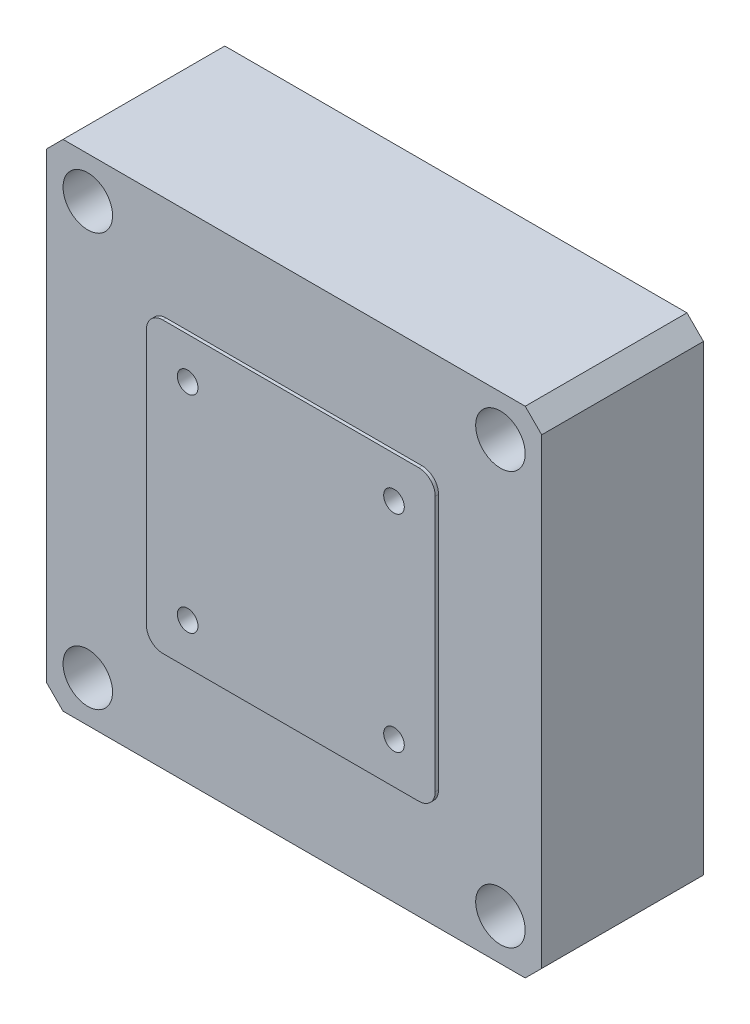
SolidWorks part; units mm, degrees
ref_plane "前视基准面" through (0, 0, 0) normal (0, 0, 1) x (1, 0, 0)
ref_plane "上视基准面" through (0, 0, 0) normal (0, 1, 0) x (1, 0, 0)
ref_plane "右视基准面" through (0, 0, 0) normal (1, 0, 0) x (0, 0, -1)
sketch "草图1" plane through (0, 0, 0) normal (0, 0, 1) x (1, 0, 0)
  line L1 (-30, 30) -> (30, 30)
  line L2 (-30, 30) -> (-30, -30)
  line L3 (-30, -30) -> (30, -30)
  line L4 (30, 30) -> (30, -30)
  line L5 (-30, 30) -> (30, -30) construction
  line L6 (-30, -30) -> (30, 30) construction
  point P0 (0, 0)
  dimension "D1" = 60
extrude "凸台-拉伸1" add sketch "草图1" along normal blind 19.6
chamfer "倒角1" distance 2 angle 45 4 edges at (-30, -30, 9.8) (30, -30, 9.8) (30, 30, 9.8) (-30, 30, 9.8)
sketch "草图2" plane through (0, 0, 19.6) normal (0, 0, 1) x (1, 0, 0)
  line L1 (-17.5, 17.5) -> (17.5, 17.5)
  line L2 (-17.5, 17.5) -> (-17.5, -17.5)
  line L3 (-17.5, -17.5) -> (17.5, -17.5)
  line L4 (17.5, 17.5) -> (17.5, -17.5)
  line L5 (-17.5, 17.5) -> (17.5, -17.5) construction
  line L6 (-17.5, -17.5) -> (17.5, 17.5) construction
  point P0 (0, 0)
  dimension "D1" = 35
extrude "凸台-拉伸2" add sketch "草图2" along normal blind 0.4
fillet "圆角1" radius 2 4 edges at (17.5, -17.5, 19.8) (-17.5, -17.5, 19.8) (17.5, 17.5, 19.8) (-17.5, 17.5, 19.8)
sketch "草图3" plane through (0, 0, 19.6) normal (0, 0, 1) x (1, 0, 0)
  line L1 (-25, 25) -> (25, 25) construction
  line L2 (-25, 25) -> (-25, -25) construction
  line L3 (-25, -25) -> (25, -25) construction
  line L4 (25, 25) -> (25, -25) construction
  line L5 (-25, 25) -> (25, -25) construction
  line L6 (-25, -25) -> (25, 25) construction
  point P0 (0, 0)
  dimension "D1" = 50
sketch "草图4" plane through (0, 0, 20) normal (0, 0, 1) x (1, 0, 0)
  line L0 (-25, -25) -> (25, 25) construction
  line L1 (-12.5, -12.5) -> (12.5, -12.5) construction
  line L2 (-12.5, -12.5) -> (-12.5, 12.5) construction
  line L3 (-12.5, 12.5) -> (12.5, 12.5) construction
  line L4 (12.5, -12.5) -> (12.5, 12.5) construction
  line L5 (-12.5, -12.5) -> (12.5, 12.5) construction
  line L6 (-12.5, 12.5) -> (12.5, -12.5) construction
  point P0 (0, 0)
  dimension "D1" = 25
hole_wizard "孔1" positions "3D草图1" profile "草图5" legacy end condition through all
sketch3d "3D草图1"
  point P0 (-25, 25, 19.6)
  point P3 (25, 25, 19.6)
  point P6 (-25, -25, 19.6)
  point P9 (25, -25, 19.6)
sketch "草图5" plane through (-25, 25, 19.6) normal (1, 0, 0) x (0, -1, 0)
  line L0 (0, 0) -> (0, 19.6)
  line L1 (0, 19.6) -> (1.7, 19.6)
  line L2 (1.7, 19.6) -> (1.7, 5)
  line L3 (1.7, 5) -> (3, 5)
  line L4 (3, 5) -> (3, 0)
  line L5 (3, 0) -> (0, 0)
  line L6 (0, 110) -> (0, -10) construction
  dimension "直径" = 3.4
  dimension "深度" = 19.6
  dimension "柱坑直径" = 6
  dimension "柱坑深度" = 5
hole_wizard "M3 螺纹孔1" positions "3D草图2" profile "草图6" tap size "M3" standard "ISO"
sketch3d "3D草图2"
  point P0 (-12.5, 12.5, 20)
  point P3 (12.5, 12.5, 20)
  point P6 (12.5, -12.5, 20)
  point P9 (-12.5, -12.5, 20)
sketch "草图6" plane through (-12.5, 12.5, 20) normal (1, 0, 0) x (0, -1, 0)
  line L0 (0, 0) -> (0, 4.2511)
  line L1 (0, 4.2511) -> (1.25, 3.5)
  line L2 (1.25, 3.5) -> (1.25, 0)
  line L5 (1.25, 0) -> (0, 0)
  line L10 (0, 4.2511) -> (-1.25, 3.5) construction
  line L11 (0, -6.35) -> (0, 107.95) construction
  dimension "螺纹孔钻头直径" = 2.5
  dimension "螺纹孔钻头深度" = 3.5
  dimension "导头角度" = 118
cosmetic thread "孔螺蚊线1" parameters "D1"=3.5, "D2"=3
cosmetic thread "孔螺蚊线2" parameters "D1"=3.5, "D2"=3
cosmetic thread "孔螺蚊线3" parameters "D1"=3.5, "D2"=3
cosmetic thread "孔螺蚊线4" parameters "D1"=3.5, "D2"=3
